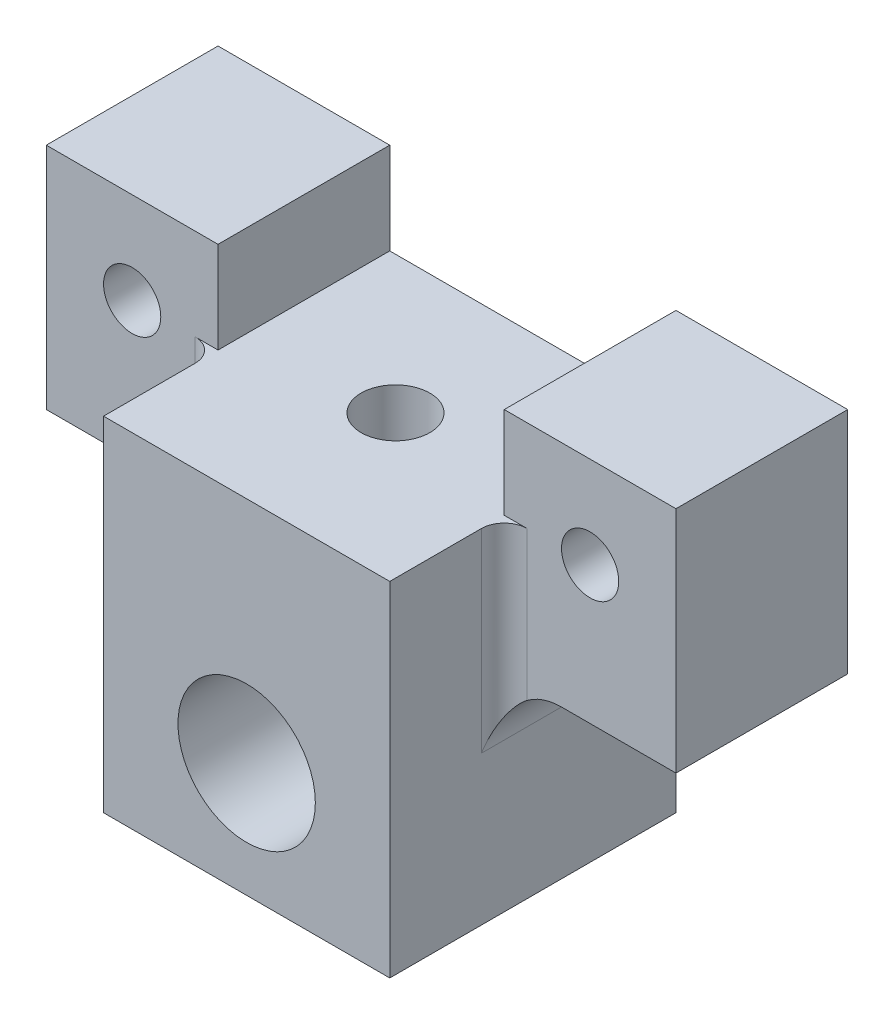
SolidWorks part; units mm, degrees
ref_plane "Front" through (0, 0, 0) normal (0, 0, 1) x (1, 0, 0)
ref_plane "Top" through (0, 0, 0) normal (0, 1, 0) x (1, 0, 0)
ref_plane "Right" through (0, 0, 0) normal (1, 0, 0) x (0, 0, -1)
sketch "Sketch1" plane through (0, 0, 0) normal (0, 1, 0) x (1, 0, 0)
  line L1 (-12.5, 12.5) -> (12.5, 12.5)
  line L2 (-12.5, 12.5) -> (-12.5, -12.5)
  line L3 (-12.5, -12.5) -> (12.5, -12.5)
  line L4 (12.5, 12.5) -> (12.5, -12.5)
  line L5 (-12.5, 12.5) -> (12.5, -12.5) construction
  line L6 (-12.5, -12.5) -> (12.5, 12.5) construction
  point P0 (0, 0)
  dimension "D1" = 25
  dimension "D2" = 25
extrude "Boss-Extrude1" add sketch "Sketch1" against normal blind 30
sketch "Sketch6" plane through (0, 0, 0) normal (0, 1, 0) x (1, 0, 0)
  line L0 (12.5, 12.5) -> (27.5, 12.5)
  line L1 (12.5, -12.5) -> (12.5, 12.5) construction
  line L2 (12.5, 12.5) -> (-12.5, 12.5) construction
  line L3 (27.5, 12.5) -> (27.5, -2.5)
  line L4 (27.5, -2.5) -> (12.5, -2.5)
  line L5 (12.5, -2.5) -> (12.5, 12.5)
  line L6 (0, -50) -> (0, 50) construction
  line L7 (-27.5, -2.5) -> (-12.5, -2.5)
  line L8 (-27.5, 12.5) -> (-27.5, -2.5)
  line L9 (-12.5, 12.5) -> (-27.5, 12.5)
  line L10 (-12.5, -2.5) -> (-12.5, 12.5)
  dimension "D1" = 15
  dimension "D2" = 15
extrude "Boss-Extrude2" add sketch "Sketch6" along normal blind 8 and the other way blind 12
sketch "Sketch3" plane through (0, 0, 0) normal (0, 0, 1) x (1, 0, 0)
  line L1 (0, -50) -> (0, 50) construction
  circle A1 centre (0, -20) radius 2.5
  circle A2 centre (20, 0) radius 2.5
  circle A4 centre (-20, 0) radius 2.5
  point P7 (0, 0)
  point P8 (0, 0)
  dimension "D1" = 5
  dimension "D3" = 20
  dimension "D2" = 20
extrude "Cut-Extrude1" cut sketch "Sketch3" against normal through all both and the other way through all
sketch "Sketch5" plane through (0, 0, 12.5) normal (0, 0, 1) x (1, 0, 0)
  circle A0 centre (0, -20) radius 6
  dimension "D1" = 12
extrude "Cut-Extrude4" cut sketch "Sketch5" against normal offset from surface (11 mm away) 14 up to face at (22.5, 0, -12.5)
sketch "Sketch2" plane through (0, 0, 0) normal (0, 1, 0) x (1, 0, 0)
  line L0 (12.5, 12.5) -> (-12.5, 12.5) construction
  circle A0 centre (0, 0.5) radius 3
  dimension "D1" = 6
  dimension "D2" = 12
extrude "Cut-Extrude6" cut sketch "Sketch2" against normal through all
sketch "Sketch4" plane through (0, -30, 0) normal (0, -1, 0) x (1, 0, 0)
  circle A0 centre (0, -0.5) radius 4.25
  circle A1 centre (0, -0.5) radius 3 construction
  point P3 (0, -0.5)
  dimension "D1" = 8.5
extrude "Cut-Extrude3" cut sketch "Sketch4" against normal blind 17.5
fillet "Fillet1" radius 5 2 edges at (-12.5, -12, -5) (12.5, -12, -5)
fillet "Fillet2" radius 2 2 edges at (-12.5, -8.5, 2.5) (12.5, -8.5, 2.5)
